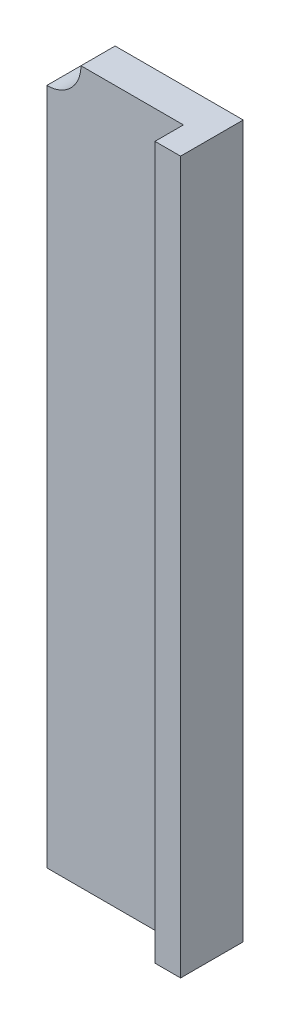
SolidWorks part; units mm, degrees
ref_plane "Alzado" through (0, 0, 0) normal (0, 0, 1) x (1, 0, 0)
ref_plane "Planta" through (0, 0, 0) normal (0, 1, 0) x (1, 0, 0)
ref_plane "Vista lateral" through (0, 0, 0) normal (1, 0, 0) x (0, 0, -1)
sketch "Croquis1" plane through (0, 0, 0) normal (0, 0, 1) x (1, 0, 0)
  line L1 (0, 0) -> (28.5, 0)
  line L2 (0, 0) -> (0, 125)
  line L3 (0, 125) -> (28.5, 125)
  line L4 (28.5, 0) -> (28.5, 125)
  dimension "D1" = 28.5
  dimension "D2" = 125
extrude "Saliente-Extruir1" add sketch "Croquis1" along normal blind 6
sketch "Croquis2" plane through (0, 0, 6) normal (0, 0, 1) x (1, 0, 0)
  line L0 (28.5, 125) -> (0, 125) construction
  line L1 (28.5, 0) -> (24, 0)
  line L2 (28.5, 0) -> (28.5, 125)
  line L3 (28.5, 125) -> (24, 125)
  line L4 (24, 0) -> (24, 125)
  dimension "D1" = 4.5
extrude "Saliente-Extruir2" add sketch "Croquis2" along normal blind 5
sketch "Croquis3" plane through (0, 0, 6) normal (0, 0, 1) x (1, 0, 0)
  circle A0 centre (0, 125) radius 6
  dimension "D1" = 12
extrude "Cortar-Extruir1" cut sketch "Croquis3" against normal through all
